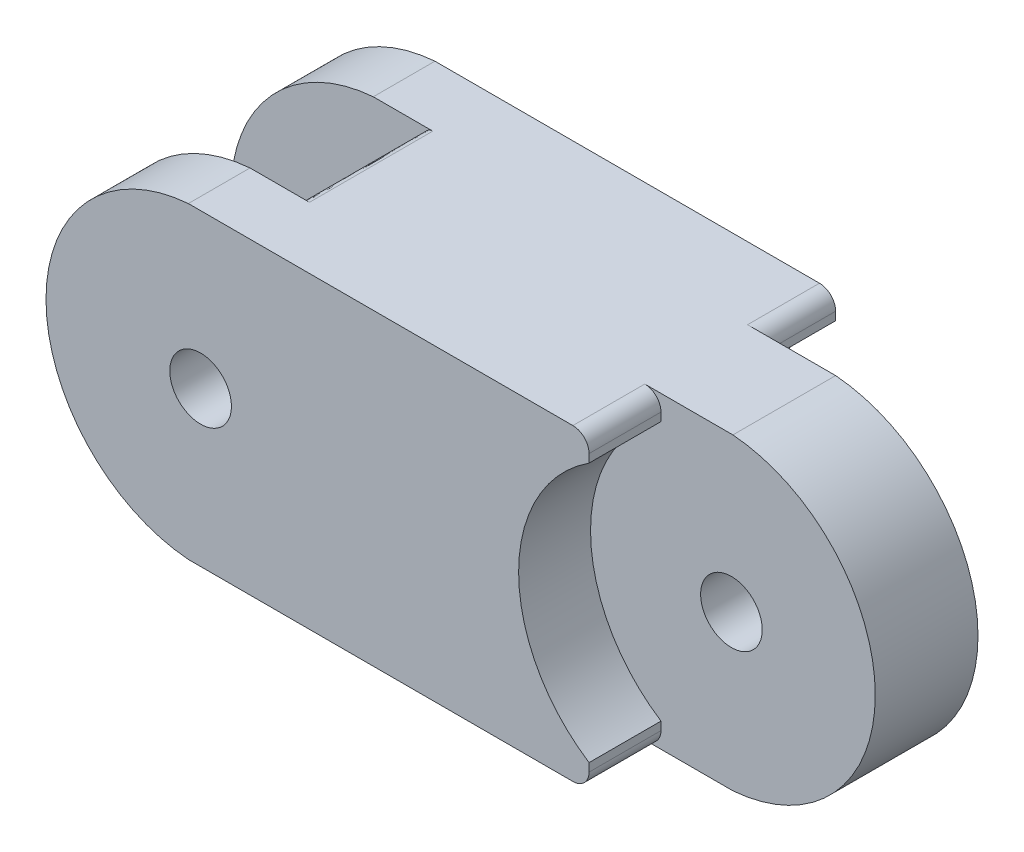
SolidWorks part; units mm, degrees
material "ABS PC"
ref_plane "Front Plane" through (0, 0, 0) normal (0, 0, 1) x (1, 0, 0)
ref_plane "Top Plane" through (0, 0, 0) normal (0, 1, 0) x (1, 0, 0)
ref_plane "Right Plane" through (0, 0, 0) normal (1, 0, 0) x (0, 0, -1)
sketch "Sketch1" plane through (0, 0, 0) normal (0, 1, 0) x (1, 0, 0)
  line L1 (-14.605, -7.62) -> (14.605, -7.62)
  line L2 (-14.605, -7.62) -> (-14.605, 7.62)
  line L3 (-14.605, 7.62) -> (14.605, 7.62)
  line L4 (14.605, -7.62) -> (14.605, 7.62)
  line L5 (-14.605, -7.62) -> (14.605, 7.62) construction
  line L6 (-14.605, 7.62) -> (14.605, -7.62) construction
  point P0 (0, 0)
  dimension "D1" = 29.21
  dimension "D2" = 15.24
extrude "Boss-Extrude1" add sketch "Sketch1" along normal blind 19.05 contours L3 L4 L1 L2
ref_plane "Plane1" through (0, 0, 0) normal (0, 0, 1) x (1, 0, 0)
sketch "Sketch3" plane through (0, 0, 0) normal (0, 0, 1) x (1, 0, 0)
  line L0 (55, 0) -> (-55, 0) construction
  line L1 (14.605, 19.05) -> (14.605, 0) construction
  line L2 (14.605, 19.05) -> (14.605, 0)
  arc A0 (14.605, 19.05) -> (14.605, 0) centre (13.8483, 9.525) cw
  dimension "D1" = 9.555
extrude "Boss-Extrude2" add sketch "Sketch3" along normal mid plane 6.35 contours A0 L2
sketch "Sketch6" plane through (0, 0, 7.62) normal (0, 0, 1) x (1, 0, 0)
  line L0 (8.3875, 0) -> (-8.3875, 0) construction
  line L1 (-14.605, 19.05) -> (-14.605, 0) construction
  line L2 (-14.605, 19.05) -> (-14.605, 0)
  arc A0 (-14.605, 19.05) -> (-14.605, 0) centre (-13.8483, 9.525) ccw
  dimension "D1" = 9.555
extrude "Boss-Extrude3" add sketch "Sketch6" along direction (0, 0, -1) on the side against the normal blind 3.81 contours A0 L2
pattern_linear "LPattern1" count 2 spacing 11.43 along (0, 0, -1) of "Boss-Extrude3"
sketch "Sketch7" plane through (0, 0, 0) normal (0, 0, 1) x (1, 0, 0)
  line L0 (23.4033, 9.525) -> (-23.4033, 9.525) construction
  circle A0 centre (-13.8483, 9.525) radius 1.905
  arc A1 (14.605, 0) -> (14.605, 19.05) centre (13.8483, 9.525) ccw construction
  arc A2 (-14.605, 19.05) -> (-14.605, 0) centre (-13.8483, 9.525) ccw construction
  dimension "D1" = 3.81
extrude "Cut-Extrude2" cut sketch "Sketch7" against normal through all both and the other way through all
ref_plane "Plane2" through (0, 0, 6.35) normal (0, 0, 1) x (1, 0, 0)
sketch "Sketch9" plane through (0, 0, 6.35) normal (0, 0, 1) x (1, 0, 0)
  line L0 (8.3875, 0) -> (-8.3875, 0) construction
  line L1 (14.605, 19.05) -> (14.605, 0) construction
  line L2 (14.605, 19.05) -> (14.605, 0)
  arc A0 (14.605, 19.05) -> (14.605, 0) centre (15.3617, 9.525) ccw
  dimension "D1" = 9.555
extrude "Cut-Extrude4" cut sketch "Sketch9" along normal blind 2.794 and the other way blind 3.175 contours A0 L2
ref_plane "Plane3" through (0, 0, -9.017) normal (0, 0, 1) x (1, 0, 0)
sketch "Sketch11" plane through (0, 0, -9.017) normal (0, 0, 1) x (1, 0, 0)
  line L0 (8.3875, 0) -> (-8.3875, 0) construction
  line L1 (14.605, 19.05) -> (14.605, 0)
  arc A0 (14.605, 19.05) -> (14.605, 0) centre (15.3617, 9.525) ccw
  arc A1 (14.605, 19.05) -> (14.605, 0) centre (15.3617, 9.525) ccw construction
  dimension "D1" = 9.555
extrude "Cut-Extrude5" cut sketch "Sketch11" along normal blind 5.842 contours A0 L1
sketch "Sketch12" plane through (0, 0, 0) normal (0, 0, 1) x (1, 0, 0)
  line L0 (8.3875, 0) -> (-8.3875, 0) construction
  line L1 (-14.605, 19.05) -> (-14.605, 0)
  arc A0 (-14.605, 19.05) -> (-14.605, 0) centre (-15.3617, 9.525) cw
  arc A1 (-14.605, 19.05) -> (-14.605, 0) centre (-13.8483, 9.525) ccw construction
  dimension "D1" = 9.555
extrude "Cut-Extrude6" cut sketch "Sketch12" against normal mid plane 7.62
fillet "Fillet2" radius 0.5 2 edges at (-14.605, 0, 0) (-14.605, 19.05, 0)
hole_wizard "CBORE for #6 Pan Head Machine Screw1" positions "Sketch14" profile "Sketch13" counterbore size "#6" standard "ANSI Inch"
sketch "Sketch14" plane through (0, 0, -7.62) normal (0, 0, -1) x (-1, 0, 0)
  point P0 (13.8483, 9.525)
sketch "Sketch13" plane through (-13.8483, 9.525, -7.62) normal (1, 0, 0) x (0, 1, 0)
  line L0 (0, 0) -> (0, 15.245)
  line L1 (0, 15.245) -> (1.875, 15.245)
  line L3 (1.875, 15.245) -> (1.875, 2.032)
  line L4 (1.875, 2.032) -> (3.75, 2.032)
  line L5 (3.75, 2.032) -> (3.75, 0)
  line L7 (3.75, 0) -> (0, 0)
  line L11 (0, -6.35) -> (0, 107.95) construction
  dimension "Thru Hole Dia." = 3.75
  dimension "Thru Hole Depth" = 15.245
  dimension "C'Bore Dia." = 7.5
  dimension "C'Bore Depth" = 2.032
sketch "Sketch15" [suppressed] plane through (0, 0, -7.62) normal (0, 0, -1) x (-1, 0, 0)
  circle A0 centre (13.8483, 9.525) radius 2.5
  circle A1 centre (13.8483, 9.525) radius 1.905 construction
  dimension "D1" = 5
extrude "Cut-Extrude7" [suppressed] cut sketch "Sketch15" against normal up to surface (3.81 mm away) contours A0
fillet "Fillet3" [suppressed] radius 0.5
sketch "Sketch16" plane through (0, 0, 6.35) normal (0, 0, 1) x (1, 0, 0)
  circle A0 centre (14.5133, 9.525) radius 1.905
  arc A1 (14.605, 0) -> (14.605, 19.05) centre (13.8483, 9.525) ccw construction
  point P11 (23.4033, 9.525)
  dimension "D1" = 8.89
  dimension "D2" = 3.81
  dimension "D3" = 17.3598
extrude "Cut-Extrude8" cut sketch "Sketch16" against normal through all both and the other way through all contours A0
sketch "Sketch17" plane through (0, 19.05, 0) normal (0, 1, 0) x (1, 0, 0)
  line L0 (14.605, 7.62) -> (14.605, 3.175)
  line L1 (14.605, 3.175) -> (10.16, 3.175)
  line L2 (10.16, 3.175) -> (10.16, 7.62)
  line L3 (-14.605, 7.62) -> (14.605, 7.62) construction
  line L4 (10.16, 7.62) -> (14.605, 7.62)
  dimension "D1" = 10.16
extrude "Cut-Extrude9" cut sketch "Sketch17" against normal up to surface (19.05 mm away) up to face at (-2.1857, 0, 0.381)
pattern_linear "LPattern2" count 2 spacing 10.795 along (0, 0, -1) of "Cut-Extrude9"
fillet "Fillet4" radius 1 4 edges at (10.16, 0, 5.3975) (10.16, 0, -5.3975) (10.16, 19.05, -5.3975) (10.16, 19.05, 5.3975)
